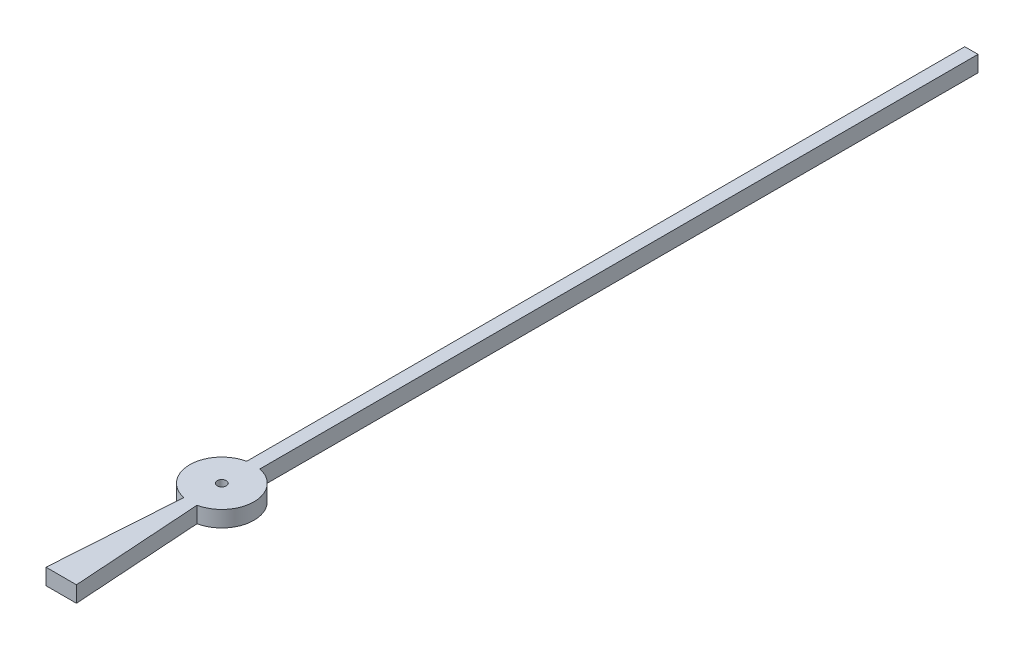
SolidWorks part; units mm, degrees
ref_plane "Front Plane" through (0, 0, 0) normal (0, 0, 1) x (1, 0, 0)
ref_plane "Top Plane" through (0, 0, 0) normal (0, 1, 0) x (1, 0, 0)
ref_plane "Right Plane" through (0, 0, 0) normal (1, 0, 0) x (0, 0, -1)
sketch "Sketch1" plane through (0, 0, 0) normal (0, 1, 0) x (1, 0, 0)
  line L0 (0.2843, -3) -> (-0.2843, -3)
  line L2 (-0.1236, 14) -> (0.1236, 14)
  line L3 (0.1236, 14) -> (0.1236, 0.5871)
  line L4 (0.1236, -0.5871) -> (0.2843, -3)
  line L6 (-0.1236, -0.5871) -> (-0.2843, -3)
  line L7 (-0.1236, 14) -> (-0.1236, 0.5871)
  arc A2 (0.1236, 0.5871) -> (0.1236, -0.5871) centre (0, 0) cw
  arc A3 (-0.1236, 0.5871) -> (-0.1236, -0.5871) centre (0, 0) ccw
extrude "Boss-Extrude1" add sketch "Sketch1" along normal blind 0.3
sketch "Sketch2" plane through (0, 0.3, 0) normal (0, 1, 0) x (1, 0, 0)
  circle A0 centre (0, 0) radius 0.085
extrude "Cut-Extrude1" cut sketch "Sketch2" against normal blind 0.3
